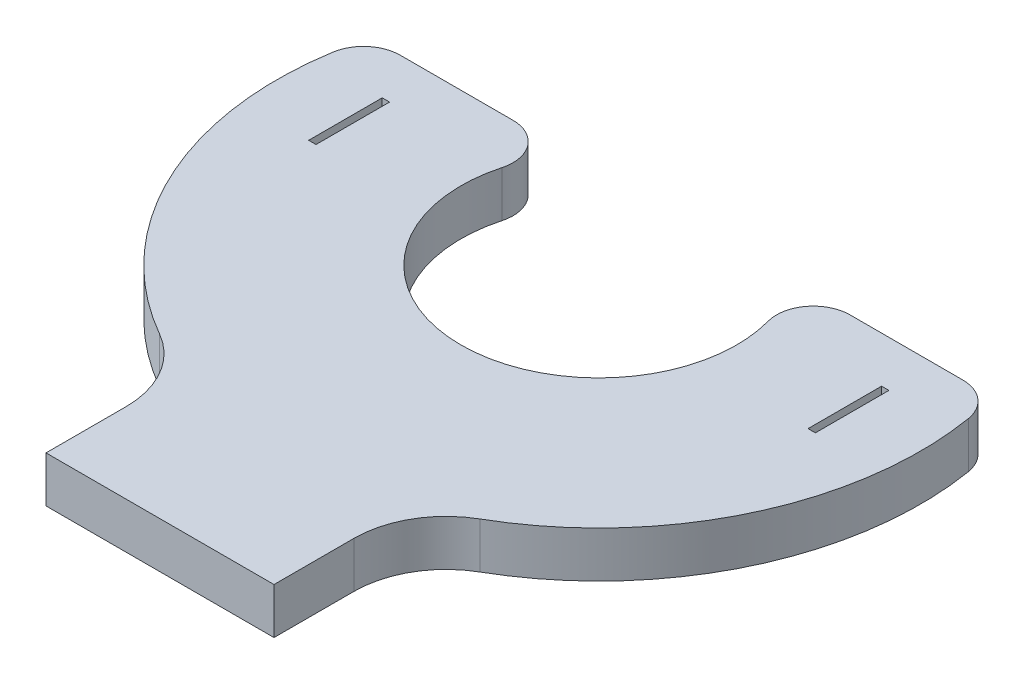
SolidWorks part; units mm, degrees
material "6061-T6 (SS)"
ref_plane "Front Plane" through (0, 0, 0) normal (0, 0, 1) x (1, 0, 0)
ref_plane "Top Plane" through (0, 0, 0) normal (0, 1, 0) x (1, 0, 0)
ref_plane "Right Plane" through (0, 0, 0) normal (1, 0, 0) x (0, 0, -1)
sketch "Sketch1" plane through (0, 0, 0) normal (0, 1, 0) x (1, 0, 0)
  line L0 (-17.2466, 0) -> (0, 0) construction
  line L1 (-17.5006, 2.54) -> (-16.9926, 2.54)
  line L2 (-17.5006, 2.54) -> (-17.5006, -2.54)
  line L3 (-17.5006, -2.54) -> (-16.9926, -2.54)
  line L4 (-16.9926, 2.54) -> (-16.9926, -2.54)
  line L5 (-17.5006, 2.54) -> (-16.9926, -2.54) construction
  line L6 (-17.5006, -2.54) -> (-16.9926, 2.54) construction
  line L7 (16.9926, 2.54) -> (17.5006, 2.54)
  line L8 (16.9926, 2.54) -> (16.9926, -2.54)
  line L9 (16.9926, -2.54) -> (17.5006, -2.54)
  line L10 (17.5006, 2.54) -> (17.5006, -2.54)
  line L11 (16.9926, 2.54) -> (17.5006, -2.54) construction
  line L12 (16.9926, -2.54) -> (17.5006, 2.54) construction
  line L13 (0, 0) -> (17.2466, 0) construction
  line L14 (-21.4776, 5.715) -> (-7.62, 5.715)
  line L15 (21.4776, 5.715) -> (7.62, 5.715)
  line L18 (-7.874, -20.7834) -> (-7.874, -30.3084)
  line L19 (-7.874, -30.3084) -> (7.874, -30.3084)
  line L20 (7.874, -20.7834) -> (7.874, -30.3084)
  arc A0 (-21.4776, 5.715) -> (-7.874, -20.7834) centre (0, 0) ccw
  arc A1 (-7.62, 5.715) -> (7.62, 5.715) centre (0, 0) ccw
  arc A2 (7.874, -20.7834) -> (21.4776, 5.715) centre (0, 0) ccw
  point P3 (-17.2466, 0)
  point P8 (17.2466, 0)
  dimension "D1" = 44.45
  dimension "D5" = 19.05
  dimension "D2" = 35.0012
  dimension "D3" = 0.508
  dimension "D4" = 5.08
  dimension "D6" = 3.175
  dimension "D7" = 15.748
  dimension "D8" = 9.525
extrude "Boss-Extrude1" add sketch "Sketch1" along normal blind 3.175
fillet "Fillet1" radius 2.54 4 edges at (-21.4776, 1.5875, -5.715) (-7.62, 1.5875, -5.715) (7.62, 1.5875, -5.715) (21.4776, 1.5875, -5.715)
fillet "Fillet2" radius 6.35 2 edges at (7.874, 1.5875, 20.7834) (-7.874, 1.5875, 20.7834)
